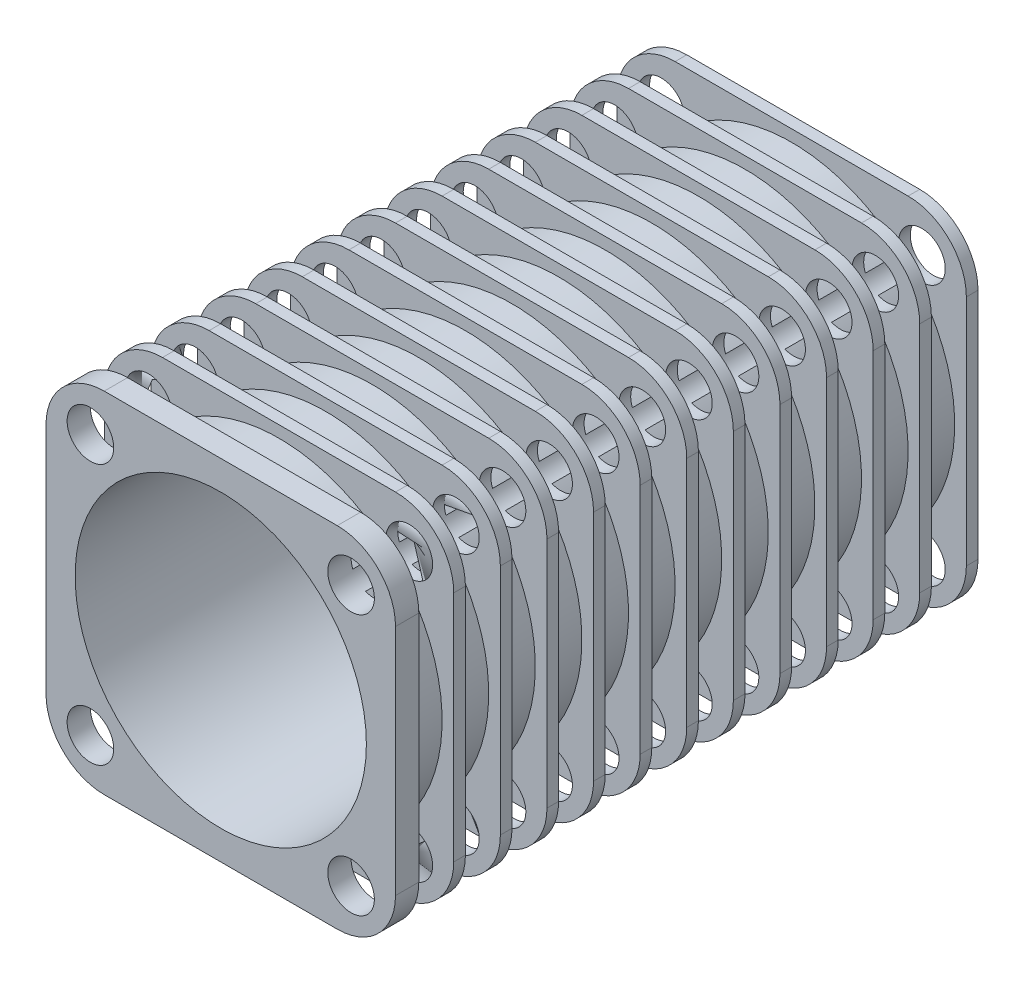
SolidWorks part; units mm, degrees
ref_plane "Front Plane" through (0, 0, 0) normal (0, 0, 1) x (1, 0, 0)
ref_plane "Top Plane" through (0, 0, 0) normal (0, 1, 0) x (1, 0, 0)
ref_plane "Right Plane" through (0, 0, 0) normal (1, 0, 0) x (0, 0, -1)
sketch "Sketch1" plane through (0, 0, 0) normal (0, 0, 1) x (1, 0, 0)
  line L1 (15, -15) -> (-15, -15)
  line L2 (15, -15) -> (15, 15)
  line L3 (15, 15) -> (-15, 15)
  line L4 (-15, -15) -> (-15, 15)
  line L5 (15, -15) -> (-15, 15) construction
  line L6 (15, 15) -> (-15, -15) construction
  circle A0 centre (0, 0) radius 12.5
  dimension "D1" = 25
  dimension "D2" = 30
  dimension "D3" = 30
extrude "Boss-Extrude1" add sketch "Sketch1" along normal blind 50
fillet "Fillet1" radius 5 4 edges at (-15, -15, 25) (15, -15, 25) (15, 15, 25) (-15, 15, 25)
sketch "Sketch4" plane through (0, 0, 0) normal (0, 1, 0) x (1, 0, 0)
  line L0 (0, 0) -> (0, -50) construction
  line L1 (10, -50) -> (-10, -50) construction
  line L2 (-14, -1) -> (-29, -1)
  line L3 (-29, -1) -> (-29, -4)
  line L4 (-29, -4) -> (-14, -4)
  line L5 (-14, -4) -> (-14, -1)
  line L6 (-10, 0) -> (-15, 0) construction
  dimension "D1" = 1
  dimension "D2" = 3
  dimension "D3" = 14
  dimension "D4" = 15
revolve "Cut-Revolve1" cut sketch "Sketch4" angle 360 about L0
pattern_linear "LPattern4" count 12 spacing 4 along (0, 0, 1) of "Cut-Revolve1"
sketch "Sketch9" plane through (0, 0, 50) normal (0, 0, 1) x (1, 0, 0)
  line L0 (-13.5355, 13.5355) -> (-8.8388, 8.8388) construction
  arc A0 (-10, 15) -> (-15, 10) centre (-10, 10) ccw construction
  circle A1 centre (0, 0) radius 12.5 construction
  circle A2 centre (-11.1872, 11.1872) radius 2
  dimension "D1" = 4
extrude "Cut-Extrude1" cut sketch "Sketch9" against normal through all
pattern_circular "CirPattern1" count 4 over 360 about axis through (0, 0, 0) along (0, 0, 1) of "Cut-Extrude1"
